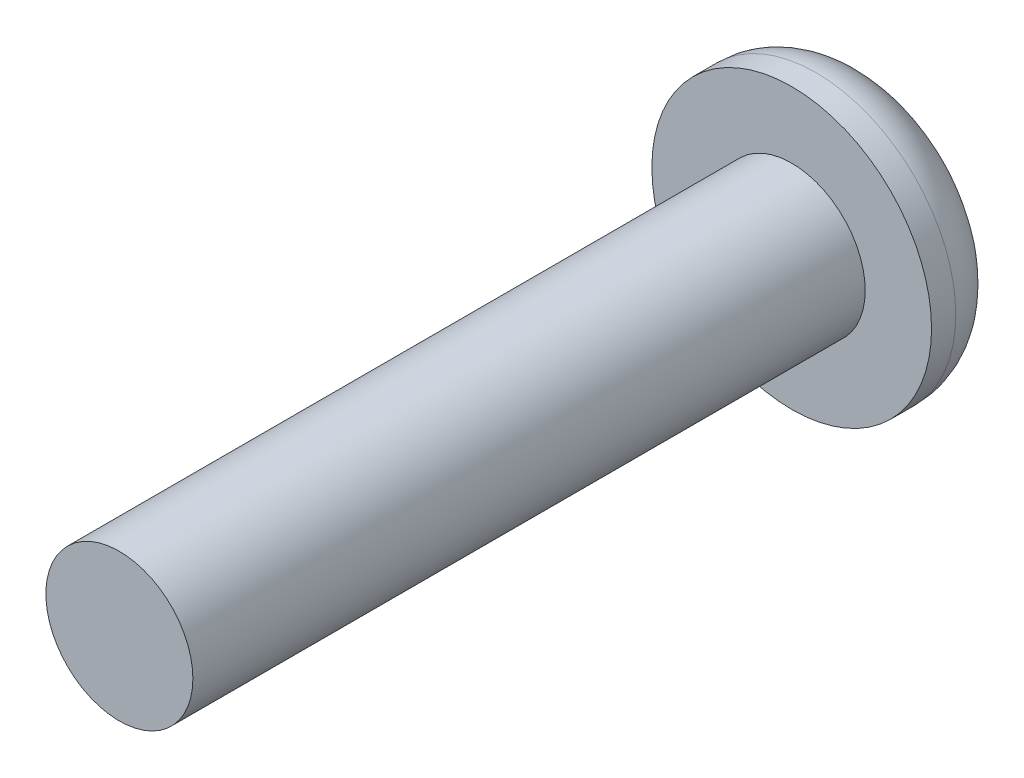
SolidWorks part; units mm, degrees
ref_plane "Front Plane" through (0, 0, 0) normal (0, 0, 1) x (1, 0, 0)
ref_plane "Top Plane" through (0, 0, 0) normal (0, 1, 0) x (1, 0, 0)
ref_plane "Right Plane" through (0, 0, 0) normal (1, 0, 0) x (0, 0, -1)
sketch "Sketch1" plane through (0, 0, 0) normal (0, 0, 1) x (1, 0, 0)
  circle A0 centre (0, 0) radius 3.9624
  dimension "D1" = 7.9248
extrude "Extrude1" add sketch "Sketch1" along normal blind 2.2098
fillet "Fillet1" radius 1.524 1 edges at (3.9624, 0, 0)
sketch "Sketch2" plane through (0, 0, 2.2098) normal (0, 0, 1) x (1, 0, 0)
  circle A0 centre (0, 0) radius 2.0828
  dimension "D1" = 4.1656
extrude "Extrude2" add sketch "Sketch2" along normal blind 19.05
sketch "Sketch3" plane through (0, 0, 0) normal (0, 0, -1) x (-1, 0, 0)
  line L1 (0.709, 1.1779) -> (-0.6656, 1.203)
  line L3 (-0.6656, 1.203) -> (-1.3746, 0.0251)
  line L5 (-1.3746, 0.0251) -> (-0.709, -1.1779)
  line L6 (-0.709, -1.1779) -> (0.6656, -1.203)
  line L7 (0.6656, -1.203) -> (1.3746, -0.0251)
  line L8 (1.3746, -0.0251) -> (0.709, 1.1779)
  circle A1 centre (0, 0) radius 1.1906 construction
  point P0 (0, 0)
  point P8 (0, 0)
  dimension "D1" = 2.3813
extrude "Extrude3" cut sketch "Sketch3" against normal blind 1.016
